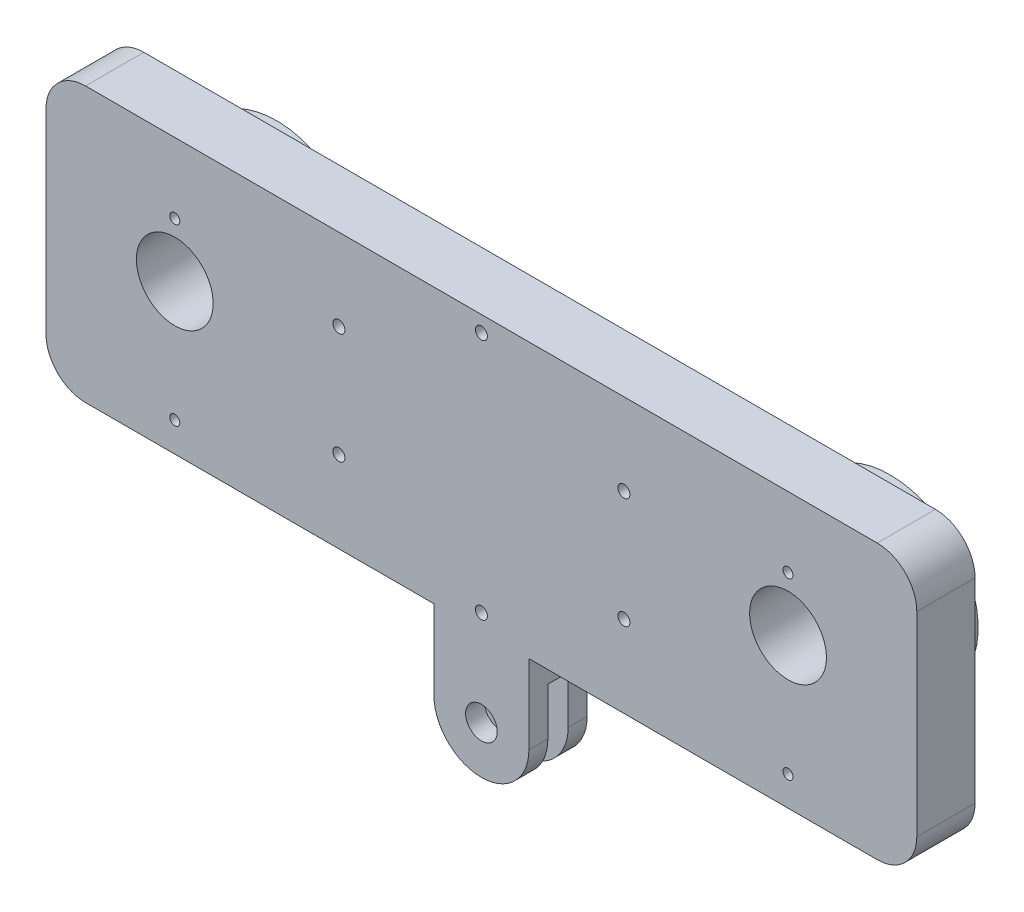
SolidWorks part; units mm, degrees
material "ABS"
ref_plane "Front Plane" through (0, 0, 0) normal (0, 0, 1) x (1, 0, 0)
ref_plane "Top Plane" through (0, 0, 0) normal (0, 1, 0) x (1, 0, 0)
ref_plane "Right Plane" through (0, 0, 0) normal (1, 0, 0) x (0, 0, -1)
sketch "Sketch1" plane through (0, 0, 0) normal (1, 0, 0) x (0, 0, -1)
  line L0 (-4.6736, 0) -> (-4.6736, 5.08)
  line L1 (-4.6736, 5.08) -> (4.6736, 5.08)
  line L2 (4.6736, 5.08) -> (4.6736, 0)
  line L3 (0, 0) -> (0, -15.24) construction
  line L4 (-1.6256, 0) -> (-1.6256, -15.24)
  line L5 (1.6256, 0) -> (1.6256, -15.24)
  line L6 (-4.6736, 0) -> (-4.6736, -15.24)
  line L7 (4.6736, 0) -> (4.6736, -15.24)
  line L8 (-4.6736, -15.24) -> (-1.6256, -15.24)
  line L9 (1.6256, -15.24) -> (4.6736, -15.24)
  line L10 (-1.6256, 0) -> (1.6256, 0)
  dimension "D2" = 5.08
  dimension "D8" = 3.048
  dimension "D9" = 3.048
  dimension "D10" = 15.24
  dimension "D6" = 1.6256
  dimension "D7" = 1.6256
extrude "Boss-Extrude1" add sketch "Sketch1" against normal blind 15.24
sketch "Sketch2" plane through (0, 0, 4.6736) normal (0, 0, 1) x (1, 0, 0)
  line L0 (-7.62, 0) -> (-7.62, -15.24) construction
  line L2 (-15.24, -15.24) -> (0, -15.24) construction
  line L3 (0, 5.08) -> (0, -15.24) construction
  line L4 (-15.24, -7.62) -> (-15.24, 0)
  line L5 (-15.24, 0) -> (0, 0)
  line L6 (0, 0) -> (0, -7.62)
  circle A0 centre (-7.62, -7.62) radius 2.54
  arc A1 (-15.24, -7.62) -> (0, -7.62) centre (-7.62, -7.62) ccw
  line M1 (0, -15.24) -> (0, 5.08)
  line M3 (-15.24, 5.08) -> (-15.24, -15.24)
  line M4 (-15.24, -15.24) -> (0, -15.24)
  dimension "D1" = 5.08
extrude "Cut-Extrude1" cut sketch "Sketch2" against normal through all contours L0 A0 | A0 L0 | A1 M3 M4 | A1 M4 M1
sketch "Sketch3" plane through (0, 0, 4.6736) normal (0, 0, 1) x (1, 0, 0)
  line L0 (-15.24, 5.08) -> (0, 5.08) construction
  line L1 (-77.47, 5.08) -> (62.23, 5.08)
  line L2 (-77.47, 5.08) -> (-77.47, 49.08)
  line L3 (-77.47, 49.08) -> (62.23, 49.08)
  line L4 (62.23, 5.08) -> (62.23, 49.08)
  line L6 (-15.24, 5.08) -> (0, 5.08) construction
  point P6 (-7.62, 5.08)
  point P9 (-7.62, 5.08)
  dimension "D1" = 139.7
  dimension "D3" = 44
extrude "Boss-Extrude2" add sketch "Sketch3" against normal up to surface (9.3472 mm away) up to face at (-5.08, -7.62, -4.6736)
fillet "Fillet1" radius 6.35 4 edges at (-77.47, 5.08, 0) (-77.47, 49.08, 0) (62.23, 5.08, 0) (62.23, 49.08, 0)
sketch "Sketch7" plane through (0, 0, -4.6736) normal (0, 0, -1) x (-1, 0, 0)
  line L0 (77.47, 42.73) -> (77.47, 11.43) construction
  line L1 (-55.88, 49.08) -> (71.12, 49.08) construction
  circle A0 centre (-41.57, 29.08) radius 6.1595
  circle A1 centre (56.81, 29.08) radius 6.1595
  dimension "D4" = 20
  dimension "D1" = 12.319
  dimension "D2" = 20.66
  dimension "D3" = 119.04
extrude "Cut-Extrude2" cut sketch "Sketch7" against normal through all
sketch "Sketch6" plane through (0, 0, 4.6736) normal (0, 0, 1) x (1, 0, 0)
  line L2 (-77.47, 42.73) -> (-77.47, 11.43) construction
  line L3 (55.88, 49.08) -> (-71.12, 49.08) construction
  line L4 (-77.47, 42.73) -> (-77.47, 11.43) construction
  line L5 (55.88, 49.08) -> (-71.12, 49.08) construction
  circle A0 centre (-30.48, 35.97) radius 0.9652
  circle A2 centre (-30.48, 18.19) radius 0.9652
  circle A4 centre (15.24, 35.97) radius 0.9652
  circle A6 centre (15.24, 18.19) radius 0.9652
  circle A7 centre (-7.62, 46.511) radius 0.9652
  circle A8 centre (-7.62, 7.649) radius 0.9652
  dimension "D1" = 1.9304
  dimension "D6" = 69.85
  dimension "D2" = 46.99
  dimension "D3" = 92.71
  dimension "D4" = 13.11
  dimension "D5" = 30.89
  dimension "D7" = 2.569
  dimension "D8" = 41.431
extrude "Cut-Extrude3" cut sketch "Sketch6" against normal blind 5.588
sketch "Sketch8" plane through (0, 0, 4.6736) normal (0, 0, 1) x (1, 0, 0)
  line L1 (-77.47, 42.73) -> (-77.47, 11.43) construction
  line L2 (55.88, 49.08) -> (-71.12, 49.08) construction
  circle A4 centre (-56.81, 9.83) radius 0.8064
  circle A5 centre (-56.81, 37.83) radius 0.8064
  circle A6 centre (41.57, 9.83) radius 0.8065
  circle A7 centre (41.57, 37.83) radius 0.8065
  dimension "D1" = 1.6129
  dimension "D2" = 20.66
  dimension "D3" = 119.04
  dimension "D4" = 11.25
  dimension "D5" = 39.25
extrude "Cut-Extrude4" cut sketch "Sketch8" against normal blind 5.08
sketch "Sketch9" plane through (0, 0, -4.6736) normal (0, 0, -1) x (-1, 0, 0)
  line L0 (77.47, 42.73) -> (77.47, 11.43) construction
  line L1 (-55.88, 49.08) -> (71.12, 49.08) construction
  circle A0 centre (-41.57, 29.08) radius 11
  circle A1 centre (56.81, 29.08) radius 11
  circle A2 centre (-41.57, 29.08) radius 14.175
  circle A3 centre (56.81, 29.08) radius 14.175
  dimension "D1" = 22
  dimension "D2" = 28.35
  dimension "D3" = 20.66
  dimension "D4" = 119.04
  dimension "D5" = 20
extrude "Boss-Extrude5" add sketch "Sketch9" along normal blind 6.985
fillet "Fillet2" radius 2.54 2 edges at (27.395, 29.08, -4.6736) (-70.985, 29.08, -4.6736)
